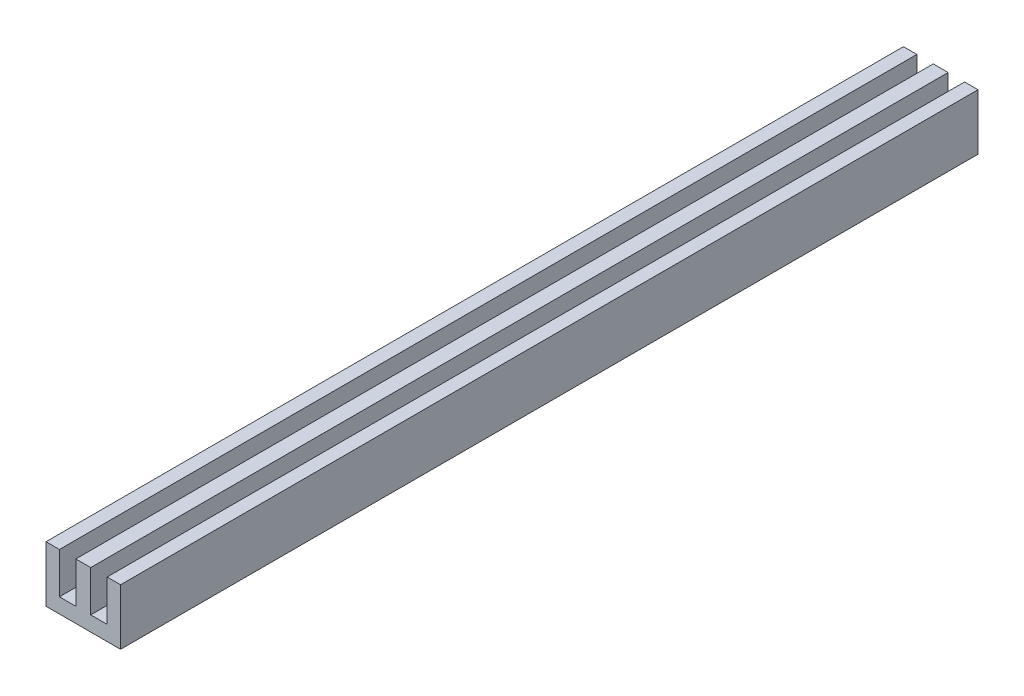
SolidWorks part; units mm, degrees
ref_plane "Plano frontal" through (0, 0, 0) normal (0, 0, 1) x (1, 0, 0)
ref_plane "Plano superior" through (0, 0, 0) normal (0, 1, 0) x (1, 0, 0)
ref_plane "Plano direito" through (0, 0, 0) normal (1, 0, 0) x (0, 0, -1)
sketch "Esboço1" plane through (0, 0, 0) normal (0, 0, 1) x (1, 0, 0)
  line L0 (-5, -1.5) -> (-5.3019, -1.5)
  line L1 (-4, -1.5) -> (-4, 4)
  line L2 (-5, -1.5) -> (-7.2, -1.5)
  line L3 (-3, 4) -> (-5, 4)
  line L4 (-4, 4) -> (-4, -1.5)
  line L5 (-3, -1.5) -> (-5, -1.5)
  line L6 (-5, 4) -> (-5, -1.5)
  line L7 (1, -1.5) -> (-0.8, -1.5)
  line L8 (-4, 4) -> (-4, -1.5)
  line L9 (1, 4) -> (1, -1.5)
  line L10 (-0.8, 4) -> (1, 4)
  line L11 (-5, -1.5) -> (-5, -1.1981)
  line L12 (-0.8, -1.5) -> (-0.8, 4)
  line L13 (-7.2, -1.5) -> (-7.2, 4)
  line L14 (-7.2, 4) -> (-9, 4)
  line L15 (-9, 4) -> (-9, -1.5)
  line L16 (-9, -1.5) -> (-7.2, -1.5)
  line L17 (-3, -1.5) -> (-3, -1.1981)
  line L18 (-3, 4) -> (-3, -1.5)
  line L19 (-3, -1.5) -> (-0.8, -1.5)
  line L20 (-3, -1.5) -> (-2.6981, -1.5)
  line L21 (-9, -1.5) -> (-9, -3.5)
  line L22 (-9, -3.5) -> (1, -3.5)
  line L23 (1, -1.5) -> (1, -3.5)
  arc A0 (-5.3019, -1.5) -> (-5, -1.1981) centre (-5.3019, -1.1981) ccw
  arc A1 (-1.1017, -1.5) -> (-0.7998, -1.1981) centre (-1.1017, -1.1981) ccw
  arc A2 (-6.8983, -1.5) -> (-7.2002, -1.1981) centre (-6.8983, -1.1981) cw
  arc A3 (-2.6981, -1.5) -> (-3, -1.1981) centre (-2.6981, -1.1981) cw
  dimension "D1" = 1.8
  dimension "D2" = 2
  dimension "D3" = 5.5
  dimension "D4" = 5.5
  dimension "D5" = 2
  dimension "D6" = 10
extrude "Ressalto-extrusão1" add sketch "Esboço1" along normal blind 115 contours L15 L16 L13 L14 | L3 L6 L5 L1 | L18 L3 L1 L5 L17 | L23 L7 L19 L5 L0 L2 L16 L21 L22 | L12 L7 L9 L10
